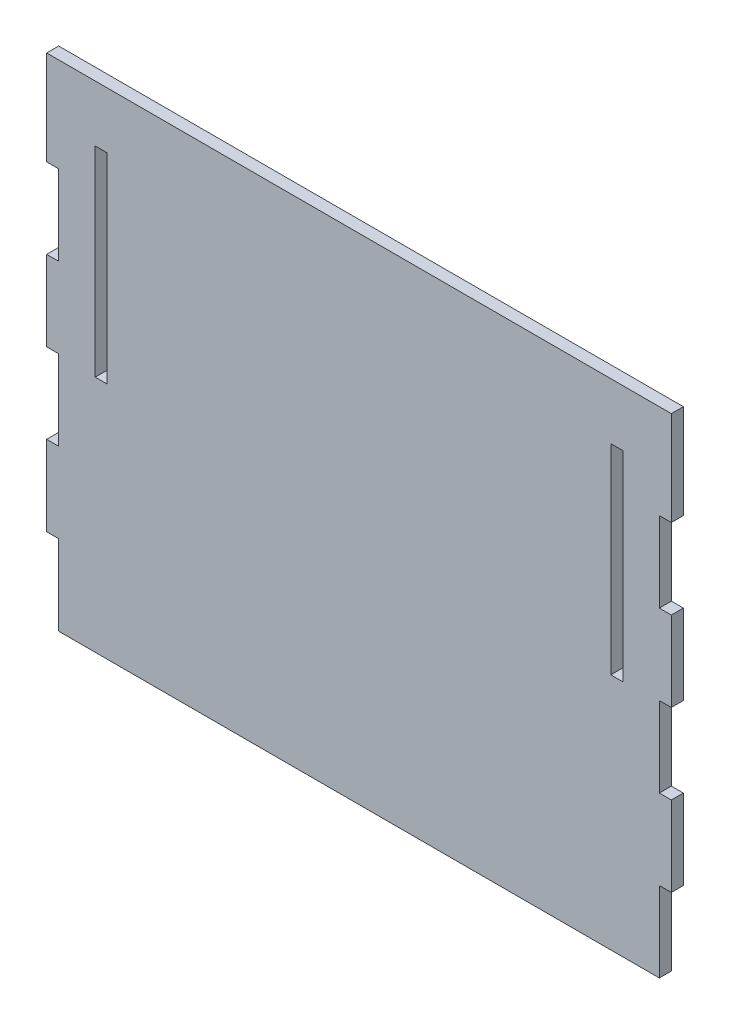
SolidWorks part; units mm, degrees
ref_plane "Front Plane" through (0, 0, 0) normal (0, 0, 1) x (1, 0, 0)
ref_plane "Top Plane" through (0, 0, 0) normal (0, 1, 0) x (1, 0, 0)
ref_plane "Right Plane" through (0, 0, 0) normal (1, 0, 0) x (0, 0, -1)
sketch "Sketch1" plane through (0, 0, 0) normal (0, 0, 1) x (1, 0, 0)
  line L1 (-302, 181.4099) -> (-2, 181.4099)
  line L2 (-302, 134.3068) -> (-302, 94.3068)
  line L3 (-302, -65.6932) -> (-2, -65.6932)
  line L4 (-2, 134.3068) -> (-2, 94.3068)
  line L5 (-308, 181.4099) -> (-308, 134.3068) construction
  line L6 (-308, 134.3068) -> (-302, 134.3068) construction
  line L8 (-302, 181.4099) -> (-308, 181.4099) construction
  line L10 (-2, 134.3068) -> (4, 134.3068) construction
  line L11 (4, 134.3068) -> (4, 181.4099) construction
  line L12 (4, 181.4099) -> (-2, 181.4099) construction
  line L14 (-2, 54.3068) -> (4, 54.3068) construction
  line L15 (4, 54.3068) -> (4, 94.3068) construction
  line L16 (4, 94.3068) -> (-2, 94.3068) construction
  line L18 (-2, -25.6932) -> (4, -25.6932) construction
  line L19 (4, -25.6932) -> (4, 14.3068) construction
  line L20 (4, 14.3068) -> (-2, 14.3068) construction
  line L21 (-308, 94.3068) -> (-308, 54.3068) construction
  line L22 (-308, 54.3068) -> (-302, 54.3068) construction
  line L24 (-302, 94.3068) -> (-308, 94.3068) construction
  line L25 (-308, 14.3068) -> (-308, -25.6932) construction
  line L26 (-308, -25.6932) -> (-302, -25.6932) construction
  line L28 (-302, 14.3068) -> (-308, 14.3068) construction
  line L29 (-308, 181.4099) -> (-308, 134.3068)
  line L30 (-308, 134.3068) -> (-302, 134.3068)
  line L32 (-302, 181.4099) -> (-308, 181.4099)
  line L34 (-2, 134.3068) -> (4, 134.3068)
  line L35 (4, 134.3068) -> (4, 181.4099)
  line L36 (4, 181.4099) -> (-2, 181.4099)
  line L38 (-2, 54.3068) -> (4, 54.3068)
  line L39 (4, 54.3068) -> (4, 94.3068)
  line L40 (4, 94.3068) -> (-2, 94.3068)
  line L42 (-2, -25.6932) -> (4, -25.6932)
  line L43 (4, -25.6932) -> (4, 14.3068)
  line L44 (4, 14.3068) -> (-2, 14.3068)
  line L45 (-308, 94.3068) -> (-308, 54.3068)
  line L46 (-308, 54.3068) -> (-302, 54.3068)
  line L48 (-302, 94.3068) -> (-308, 94.3068)
  line L49 (-308, 14.3068) -> (-308, -25.6932)
  line L50 (-308, -25.6932) -> (-302, -25.6932)
  line L52 (-302, 14.3068) -> (-308, 14.3068)
  line L53 (-302, -25.6932) -> (-302, -65.6932)
  line L54 (-302, 54.3068) -> (-302, 14.3068)
  line L55 (-2, -25.6932) -> (-2, -65.6932)
  line L56 (-2, 54.3068) -> (-2, 14.3068)
  line L66 (-277.75, 53.3068) -> (-277.75, 153.3068) construction
  line L67 (-277.75, 153.3068) -> (-283.75, 153.3068) construction
  line L68 (-283.75, 153.3068) -> (-283.75, 53.3068) construction
  line L69 (-283.75, 53.3068) -> (-277.75, 53.3068) construction
  line L70 (-20.25, 53.3068) -> (-20.25, 153.3068) construction
  line L71 (-20.25, 153.3068) -> (-26.25, 153.3068) construction
  line L72 (-26.25, 153.3068) -> (-26.25, 53.3068) construction
  line L73 (-26.25, 53.3068) -> (-20.25, 53.3068) construction
  line L74 (-277.75, 53.3068) -> (-277.75, 153.3068)
  line L75 (-277.75, 153.3068) -> (-283.75, 153.3068)
  line L76 (-283.75, 153.3068) -> (-283.75, 53.3068)
  line L77 (-283.75, 53.3068) -> (-277.75, 53.3068)
  line L78 (-20.25, 53.3068) -> (-20.25, 153.3068)
  line L79 (-20.25, 153.3068) -> (-26.25, 153.3068)
  line L80 (-26.25, 153.3068) -> (-26.25, 53.3068)
  line L81 (-26.25, 53.3068) -> (-20.25, 53.3068)
extrude "Boss-Extrude1" add sketch "Sketch1" along normal up to surface (6 mm away)
